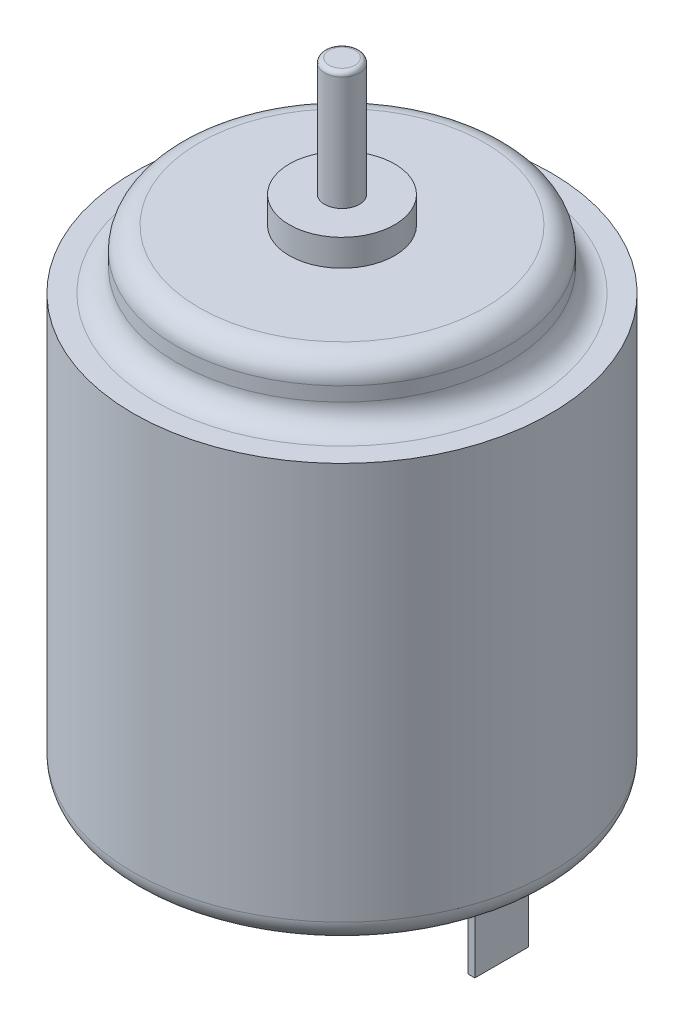
SolidWorks part; units mm, degrees
ref_plane "Front Plane" through (0, 0, 0) normal (0, 0, 1) x (1, 0, 0)
ref_plane "Top Plane" through (0, 0, 0) normal (0, 1, 0) x (1, 0, 0)
ref_plane "Right Plane" through (0, 0, 0) normal (1, 0, 0) x (0, 0, -1)
sketch "Sketch1" plane through (0, 0, 0) normal (0, 1, 0) x (1, 0, 0)
  circle A0 centre (0, 0) radius 11.8745
  dimension "D1" = 23.749
extrude "Boss-Extrude1" add sketch "Sketch1" along normal blind 23.876
sketch "Sketch2" plane through (0, 23.876, 0) normal (0, 1, 0) x (1, 0, 0)
  circle A0 centre (0, 0) radius 9.398
  dimension "D1" = 18.796
extrude "Boss-Extrude2" add sketch "Sketch2" along normal blind 3.3401
sketch "Sketch3" plane through (0, 27.2161, 0) normal (0, 1, 0) x (1, 0, 0)
  circle A0 centre (0, 0) radius 2.9972
  dimension "D1" = 5.9944
extrude "Boss-Extrude3" add sketch "Sketch3" along normal blind 1.524
sketch "Sketch4" plane through (0, 28.7401, 0) normal (0, 1, 0) x (1, 0, 0)
  circle A0 centre (0, 0) radius 0.9906
  dimension "D1" = 1.9812
extrude "Boss-Extrude4" add sketch "Sketch4" along normal blind 6.731
sketch "Sketch5" plane through (0, 0, 0) normal (0, -1, 0) x (1, 0, 0)
  circle A0 centre (0, 0) radius 4.2926
  dimension "D1" = 8.5852
extrude "Boss-Extrude5" add sketch "Sketch5" along normal blind 2.032
sketch "Sketch6" plane through (0, -2.032, 0) normal (0, -1, 0) x (1, 0, 0)
  line L0 (2.162, 3.7084) -> (-2.162, 3.7084)
  circle A1 centre (0, 0) radius 4.2926
  arc A2 (2.162, 3.7084) -> (-2.162, 3.7084) centre (0, 0) ccw
  point P1 (0, -4.2926)
  dimension "D2" = 8.001
  dimension "D1" = 0
extrude "Cut-Extrude1" cut sketch "Sketch6" against normal blind 2.032
sketch "Sketch7" plane through (0, 0, 0) normal (0, -1, 0) x (1, 0, 0)
  line L0 (0, 0) -> (0, -6.4897) construction
  line L1 (-8.6995, 1.524) -> (-9.0805, 1.524)
  line L2 (-8.6995, 1.524) -> (-8.6995, -1.524)
  line L3 (-8.6995, -1.524) -> (-9.0805, -1.524)
  line L4 (-9.0805, 1.524) -> (-9.0805, -1.524)
  line L5 (-8.6995, 1.524) -> (-9.0805, -1.524) construction
  line L6 (-8.6995, -1.524) -> (-9.0805, 1.524) construction
  line L7 (8.6995, -1.524) -> (9.0805, 1.524) construction
  line L8 (8.6995, 1.524) -> (9.0805, -1.524) construction
  line L9 (9.0805, 1.524) -> (9.0805, -1.524)
  line L10 (8.6995, -1.524) -> (9.0805, -1.524)
  line L11 (8.6995, 1.524) -> (8.6995, -1.524)
  line L12 (8.6995, 1.524) -> (9.0805, 1.524)
  point P0 (-8.89, 0)
  point P13 (8.89, 0)
  dimension "D1" = 0.381
  dimension "D2" = 3.048
  dimension "D3" = 8.89
extrude "Boss-Extrude6" add sketch "Sketch7" along normal blind 4.572
fillet "Fillet1" radius 1.27 3 edges at (0, 23.876, 9.398) (0, 27.2161, 9.398) (0, 0, 11.8745)
fillet "Fillet2" radius 0.254 1 edges at (0, 35.4711, 0.9906)
